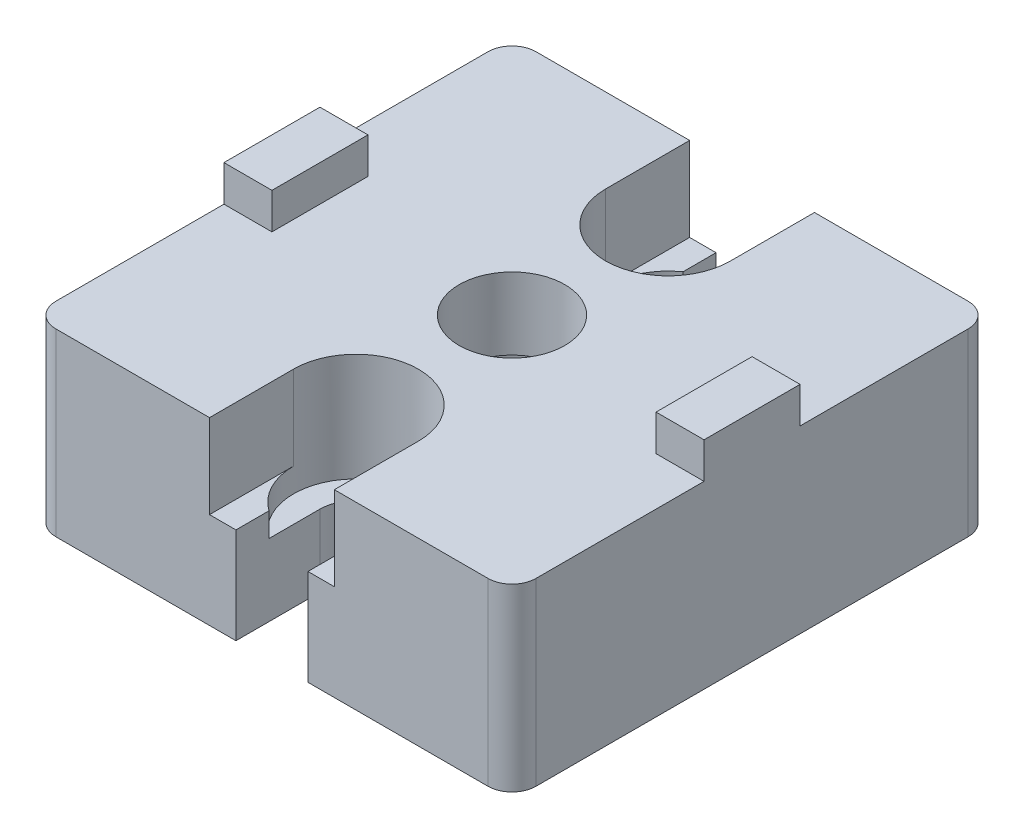
SolidWorks part; units mm, degrees
material "Алюминиевый сплав"
ref_plane "Спереди" through (0, 0, 0) normal (0, 0, 1) x (1, 0, 0)
ref_plane "Сверху" through (0, 0, 0) normal (0, 1, 0) x (1, 0, 0)
ref_plane "Справа" through (0, 0, 0) normal (1, 0, 0) x (0, 0, -1)
sketch "Эскиз1" plane through (0, 0, 0) normal (0, 1, 0) x (1, 0, 0)
  line L1 (20, 20) -> (-20, 20)
  line L2 (20, 20) -> (20, -20)
  line L3 (20, -20) -> (-20, -20)
  line L4 (-20, 20) -> (-20, -20)
  line L5 (20, 20) -> (-20, -20) construction
  line L6 (20, -20) -> (-20, 20) construction
  point P0 (0, 0)
  dimension "D1" = 40
extrude "Бобышка-Вытянуть1" add sketch "Эскиз1" along normal blind 15
sketch "Эскиз2" plane through (0, 15, 0) normal (0, 1, 0) x (1, 0, 0)
  line L0 (-20, 20) -> (-20, -20) construction
  line L1 (-16, -4) -> (-20, -4)
  line L2 (-16, -4) -> (-16, 4)
  line L3 (-16, 4) -> (-20, 4)
  line L4 (-20, -4) -> (-20, 4)
  line L5 (-16, -4) -> (-20, 4) construction
  line L6 (-16, 4) -> (-20, -4) construction
  line L7 (0, 0) -> (0, 6.185) construction
  line L8 (16, 4) -> (20, -4) construction
  line L9 (16, -4) -> (20, 4) construction
  line L10 (20, -4) -> (20, 4)
  line L11 (16, 4) -> (20, 4)
  line L12 (16, -4) -> (16, 4)
  line L13 (16, -4) -> (20, -4)
  point P0 (-18, 0)
  point P10 (0, 0)
  point P11 (-15, 1.8997)
  point P16 (18, 0)
  dimension "D1" = 4
  dimension "D2" = 8
extrude "Бобышка-Вытянуть2" add sketch "Эскиз2" along normal blind 3
sketch "Эскиз3" plane through (0, 15, 0) normal (0, 1, 0) x (1, 0, 0)
  line L0 (-3, -20) -> (-3, -13)
  line L1 (-20, -20) -> (20, -20) construction
  line L2 (3, -13) -> (3, -20)
  line L3 (3, -20) -> (-3, -20)
  line L4 (0, 0) -> (-17.3843, 0) construction
  line L5 (3, 13) -> (3, 20)
  line L6 (-3, 20) -> (-3, 13)
  line L7 (3, 20) -> (-3, 20)
  circle A0 centre (0, 0) radius 4.4
  arc A1 (-3, -13) -> (3, -13) centre (0, -13) cw
  arc A2 (-3, 13) -> (3, 13) centre (0, 13) ccw
  point P9 (0, 0)
  dimension "D1" = 8.8
  dimension "D2" = 3
  dimension "D3" = 26
extrude "Вырез-Вытянуть1" cut sketch "Эскиз3" against normal through all
sketch "Эскиз4" plane through (0, 0, 0) normal (0, -1, 0) x (1, 0, 0)
  circle A0 centre (0, 0) radius 6.9
  dimension "D1" = 13.8
extrude "Вырез-Вытянуть2" cut sketch "Эскиз4" against normal blind 9
sketch "Эскиз5" plane through (0, 15, 0) normal (0, 1, 0) x (1, 0, 0)
  line L0 (-5.2, -20) -> (-5.2, -13)
  line L1 (-20, -20) -> (-3, -20) construction
  line L2 (5.2, -13) -> (5.2, -20)
  line L3 (3, -20) -> (20, -20) construction
  line L4 (5.2, -20) -> (-5.2, -20)
  line L5 (0, 0) -> (-17.0309, 0) construction
  line L6 (5.2, 13) -> (5.2, 20)
  line L7 (-5.2, 20) -> (-5.2, 13)
  line L8 (5.2, 20) -> (-5.2, 20)
  arc A0 (-5.2, -13) -> (5.2, -13) centre (0, -13) cw
  arc A3 (-5.2, 13) -> (5.2, 13) centre (0, 13) ccw
  dimension "D1" = 5.2
extrude "Вырез-Вытянуть3" cut sketch "Эскиз5" against normal blind 7
sketch "Эскиз6" plane through (0, 8, 0) normal (0, 1, 0) x (1, 0, 0)
  circle A0 centre (0, -13) radius 5.2
  circle A1 centre (0, 13) radius 5.2
extrude "Вырез-Вытянуть4" cut sketch "Эскиз6" against normal blind 2
fillet "Скругление1" radius 2 4 edges at (-20, 7.5, -20) (20, 7.5, -20) (20, 7.5, 20) (-20, 7.5, 20)
